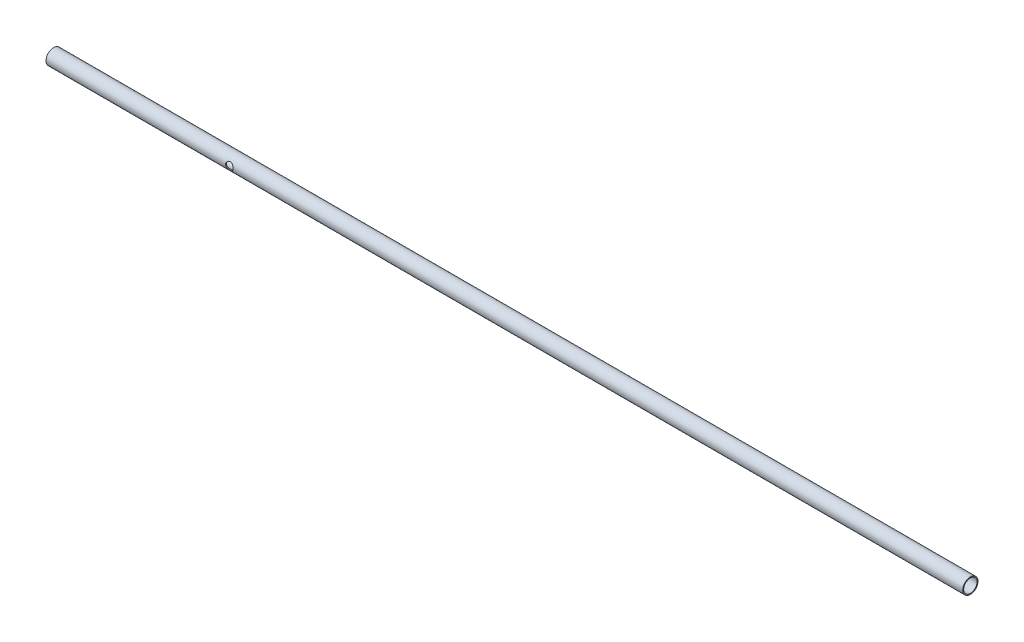
SolidWorks part; units mm, degrees
ref_plane "Front Plane" through (0, 0, 0) normal (0, 0, 1) x (1, 0, 0)
ref_plane "Top Plane" through (0, 0, 0) normal (0, 1, 0) x (1, 0, 0)
ref_plane "Right Plane" through (0, 0, 0) normal (1, 0, 0) x (0, 0, -1)
sketch "Sketch1" plane through (0, 0, 0) normal (0, 0, 1) x (1, 0, 0)
  line L0 (0, 0) -> (762, 0)
  line L1 (55, 0) -> (-55, 0) construction
  dimension "D1" = 762
sketch "Sketch2" plane through (0, 0, 0) normal (1, 0, 0) x (0, 0, -1)
  circle A0 centre (0, 0) radius 6.35
  circle A1 centre (0, 0) radius 5.5562
  dimension "D1" = 12.7
  dimension "D2" = 0.7937
sweep "Sweep1" add profiles "Sketch2" path "Sketch1"
sketch "Sketch3" plane through (0, 0, 0) normal (0, 0, 1) x (1, 0, 0)
  line L0 (0, 0) -> (152.4, 0) construction
  circle A0 centre (152.4, 0) radius 3.175
  dimension "D2" = 6.35
  dimension "D1" = 152.4
extrude "Cut-Extrude1" cut sketch "Sketch3" against normal through all and the other way through all
